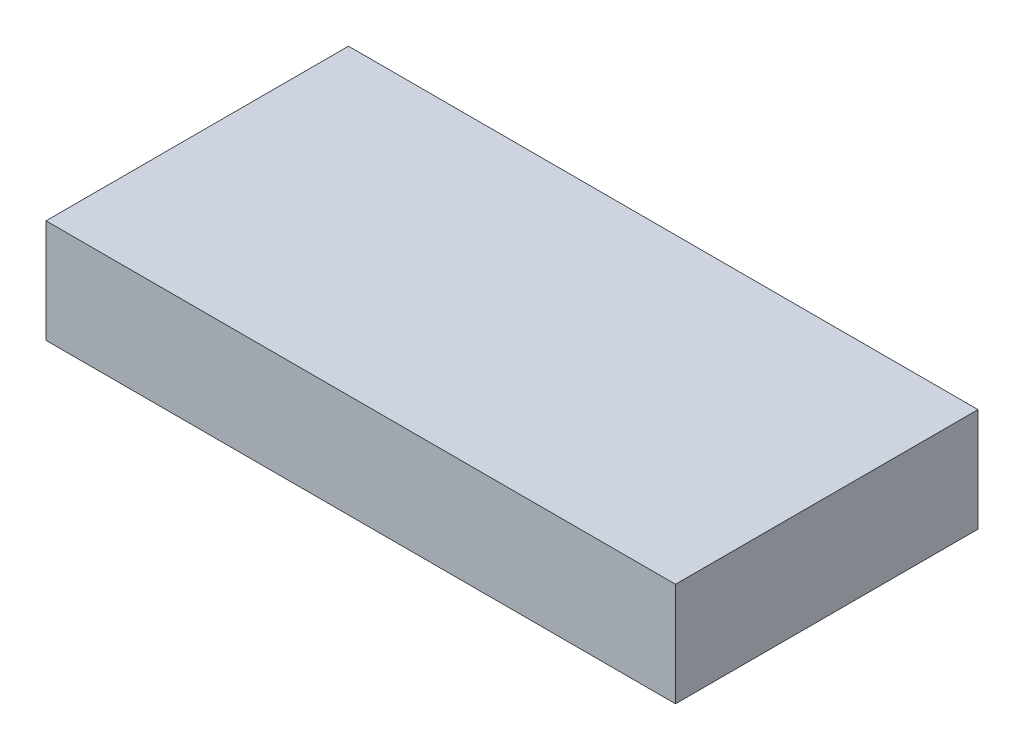
SolidWorks part; units mm, degrees
ref_plane "Front Plane" through (0, 0, 0) normal (0, 0, 1) x (1, 0, 0)
ref_plane "Top Plane" through (0, 0, 0) normal (0, 1, 0) x (1, 0, 0)
ref_plane "Right Plane" through (0, 0, 0) normal (1, 0, 0) x (0, 0, -1)
sketch "Sketch1" plane through (0, 0, 0) normal (0, 1, 0) x (1, 0, 0)
  line L1 (-183.3562, -88.1063) -> (183.3562, -88.1063)
  line L2 (-183.3562, -88.1063) -> (-183.3562, 88.1063)
  line L3 (-183.3562, 88.1063) -> (183.3562, 88.1063)
  line L4 (183.3562, -88.1063) -> (183.3562, 88.1063)
  line L5 (-183.3562, -88.1063) -> (183.3562, 88.1063) construction
  line L6 (-183.3562, 88.1063) -> (183.3562, -88.1063) construction
  point P0 (0, 0)
  dimension "D1" = 366.7125
  dimension "D2" = 176.2125
extrude "Boss-Extrude1" add sketch "Sketch1" along normal blind 60.325
